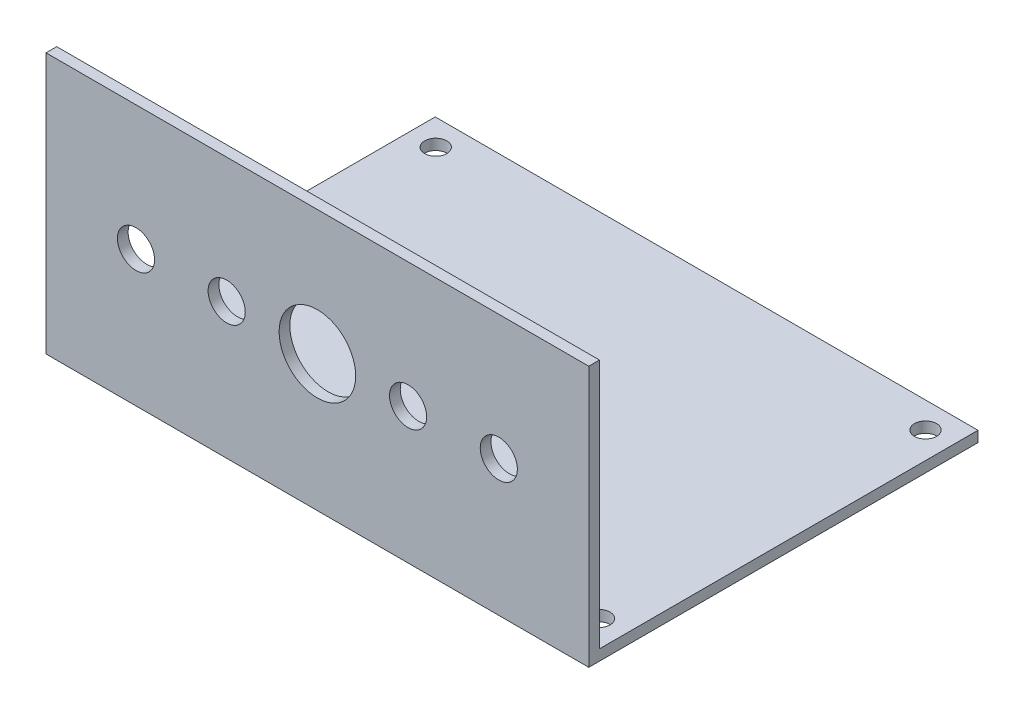
SolidWorks part; units mm, degrees
material "PTFE(普通)"
ref_plane "前视基准面" through (0, 0, 0) normal (0, 0, 1) x (1, 0, 0)
ref_plane "上视基准面" through (0, 0, 0) normal (0, 1, 0) x (1, 0, 0)
ref_plane "右视基准面" through (0, 0, 0) normal (1, 0, 0) x (0, 0, -1)
other "Configuration Table"
sketch "草图1" plane through (0, 0, 0) normal (0, 1, 0) x (1, 0, 0)
  line L1 (34.29, -22.86) -> (-34.29, -22.86) construction
  line L2 (34.29, -22.86) -> (34.29, 22.86) construction
  line L3 (34.29, 22.86) -> (-34.29, 22.86) construction
  line L4 (-34.29, -22.86) -> (-34.29, 22.86) construction
  line L5 (34.29, -22.86) -> (-34.29, 22.86) construction
  line L6 (34.29, 22.86) -> (-34.29, -22.86) construction
  line L7 (38, -26.5) -> (-38, -26.5)
  line L8 (38, -26.5) -> (38, 26.5)
  line L9 (38, 26.5) -> (-38, 26.5)
  line L10 (-38, -26.5) -> (-38, 26.5)
  line L11 (38, -26.5) -> (-38, 26.5) construction
  line L12 (38, 26.5) -> (-38, -26.5) construction
  circle A0 centre (-34.29, 22.86) radius 1.55
  circle A1 centre (-34.29, -22.86) radius 1.55
  circle A2 centre (34.29, -22.86) radius 1.55
  circle A3 centre (34.29, 22.86) radius 1.55
  point P0 (0, 0)
  point P10 (0, 0)
  dimension "D3" = 3.1
  dimension "D4" = 3.1
  dimension "D5" = 3.1
  dimension "D6" = 3.1
  dimension "D1" = 22.86
  dimension "D2" = 34.29
  dimension "D7" = 38
  dimension "D8" = 26.5
extrude "凸台-拉伸1" add sketch "草图1" along normal blind 1.5
sketch "草图2" plane through (0, 0, 26.5) normal (0, 0, 1) x (1, 0, 0)
  line L1 (-38, 1.5) -> (38, 1.5)
  line L2 (-38, 1.5) -> (-38, 0)
  line L3 (-38, 0) -> (38, 0)
  line L4 (38, 1.5) -> (38, 0)
extrude "凸台-拉伸2" add sketch "草图2" along normal blind 1.5 contours L3 L4 L1 L2
sketch "草图3" plane through (0, 1.5, 0) normal (0, 1, 0) x (1, 0, 0)
  line L0 (38, -28) -> (38, 26.5) construction
  line L1 (-38, -28) -> (38, -28)
  line L2 (-38, -28) -> (-38, -26.5)
  line L3 (-38, -26.5) -> (38, -26.5)
  line L4 (38, -28) -> (38, -26.5)
  dimension "D1" = 1.5
extrude "凸台-拉伸3" add sketch "草图3" along normal blind 35.02
sketch "草图4" plane through (0, 0, 26.5) normal (0, 0, -1) x (-1, 0, 0)
  line L0 (-38, 1.5) -> (38, 1.5) construction
  line L1 (-38, 36.52) -> (-38, 1.5) construction
  circle A0 centre (0, 19.02) radius 5.36
  circle A1 centre (-12.7, 19.02) radius 2.6
  circle A2 centre (-25.4, 19.02) radius 2.6
  circle A3 centre (12.7, 19.02) radius 2.6
  circle A4 centre (25.4, 19.02) radius 2.6
  dimension "D2" = 10.72
  dimension "D6" = 5.2
  dimension "D7" = 5.2
  dimension "D10" = 5.2
  dimension "D11" = 5.2
  dimension "D1" = 17.52
  dimension "D3" = 38
  dimension "D4" = 12.7
  dimension "D5" = 12.7
  dimension "D8" = 12.7
  dimension "D9" = 12.7
extrude "切除-拉伸1" cut sketch "草图4" against normal blind 60
